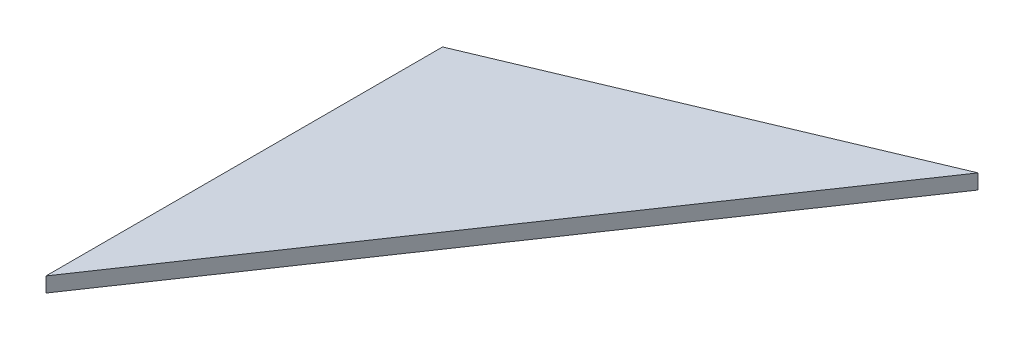
SolidWorks part; units mm, degrees
material "Plain Carbon Steel"
ref_plane "Front Plane" through (0, 0, 0) normal (0, 0, 1) x (1, 0, 0)
ref_plane "Top Plane" through (0, 0, 0) normal (0, 1, 0) x (1, 0, 0)
ref_plane "Right Plane" through (0, 0, 0) normal (1, 0, 0) x (0, 0, -1)
sketch "Sketch1" plane through (0, 0, 0) normal (0, 1, 0) x (1, 0, 0)
  line L0 (0, 0) -> (0, 127)
  line L1 (0, 127) -> (120.65, 177.8)
  line L2 (120.65, 177.8) -> (0, 0)
  dimension "D1" = 127
  dimension "D2" = 120.65
  dimension "D3" = 50.8
extrude "Boss-Extrude1" add sketch "Sketch1" along normal blind 4.7625
